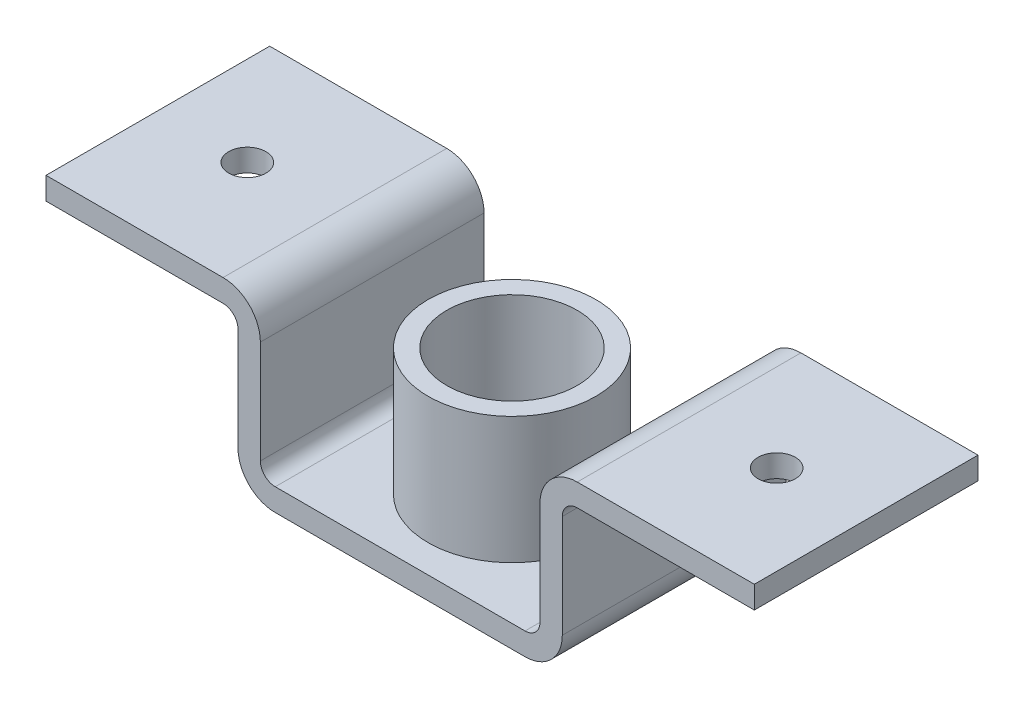
SolidWorks part; units mm, degrees
ref_plane "Front Plane" through (0, 0, 0) normal (0, 0, 1) x (1, 0, 0)
ref_plane "Top Plane" through (0, 0, 0) normal (0, 1, 0) x (1, 0, 0)
ref_plane "Right Plane" through (0, 0, 0) normal (1, 0, 0) x (0, 0, -1)
sketch "Sketch1" plane through (0, 0, 0) normal (0, 0, 1) x (1, 0, 0)
  line L0 (0, 0) -> (-167.5, 0)
  line L1 (-217.5, 50) -> (-217.5, 188)
  line L2 (-237.5, 208) -> (-475, 208)
  line L3 (0, 30) -> (-167.5, 30)
  line L4 (-187.5, 50) -> (-187.5, 188)
  line L5 (-237.5, 238) -> (-475, 238)
  line L6 (0, 0) -> (0, 353.2366) construction
  line L7 (237.5, 238) -> (475, 238)
  line L8 (187.5, 50) -> (187.5, 188)
  line L9 (0, 30) -> (167.5, 30)
  line L10 (237.4943, 208) -> (475, 208)
  line L11 (217.4551, 49.9858) -> (217.4943, 188.0057)
  line L12 (0, 0) -> (167.4551, 0)
  line L13 (0, 30) -> (-187.5, 30) construction
  line L14 (-187.5, 30) -> (-187.5, 238) construction
  line L15 (-217.5, 0) -> (-217.5, 208) construction
  line L16 (-217.5, 208) -> (-475, 208) construction
  line L17 (0, 0) -> (-217.5, 0) construction
  line L18 (-187.5, 238) -> (-475, 238) construction
  line L19 (475, 208) -> (475, 238)
  line L20 (-475, 208) -> (-475, 238)
  arc A0 (217.4943, 188.0057) -> (237.4943, 208) centre (237.4943, 188) cw
  arc A1 (167.5, 30) -> (187.5, 50) centre (167.5, 50) ccw
  arc A2 (-167.5, 30) -> (-187.5, 50) centre (-167.5, 50) cw
  arc A3 (-217.5, 188) -> (-237.5, 208) centre (-237.5, 188) ccw
  arc A4 (187.5, 188) -> (237.5, 238) centre (237.5, 188) cw
  arc A5 (167.4551, 0) -> (217.4551, 49.9858) centre (167.4551, 50) ccw
  arc A6 (-167.5, 0) -> (-217.5, 50) centre (-167.5, 50) cw
  arc A7 (-187.5, 188) -> (-237.5, 238) centre (-237.5, 188) ccw
  point P18 (217.5, 208)
  point P21 (187.5, 30)
  point P25 (-187.5, 30)
  point P29 (-217.5, 208)
  point P32 (187.5, 238)
  point P35 (217.4409, 0)
  point P42 (187.5, 119)
  dimension "D5" = 20
  dimension "D6" = 50
  dimension "D1" = 187.5
  dimension "D2" = 475
  dimension "D3" = 119
  dimension "D7" = 208
  dimension "D8" = 238
  dimension "D9" = 217.4551
  dimension "D4" = 30
extrude "Boss-Extrude1" add sketch "Sketch1" along normal blind 300
sketch "Sketch3" plane through (0, 238, 0) normal (0, 1, 0) x (1, 0, 0)
  line L0 (475, -300) -> (237.5, -300) construction
  line L1 (475, -300) -> (475, 0) construction
  circle A0 centre (355, -150) radius 25
  dimension "D1" = 50
  dimension "D2" = 150
  dimension "D3" = 120
extrude "Cut-Extrude2" cut sketch "Sketch3" against normal through all
pattern_linear "LPattern1" count 2 spacing 710 along (-1, 0, 0) of "Cut-Extrude2"
sketch "Sketch4" plane through (0, 30, 0) normal (0, 1, 0) x (1, 0, 0)
  line L0 (167.5, -300) -> (-167.5, -300) construction
  circle A0 centre (0, -150) radius 87.5
  circle A1 centre (0, -150) radius 112.5
  point P3 (0, 0)
  dimension "D1" = 225
  dimension "D2" = 175
  dimension "D3" = 150
extrude "Boss-Extrude2" add sketch "Sketch4" along normal blind 170
sketch "Sketch5" plane through (0, 30, 0) normal (0, 1, 0) x (1, 0, 0)
  circle A0 centre (0, -150) radius 37.5
  dimension "D1" = 75
extrude "Cut-Extrude3" cut sketch "Sketch5" against normal blind 170
